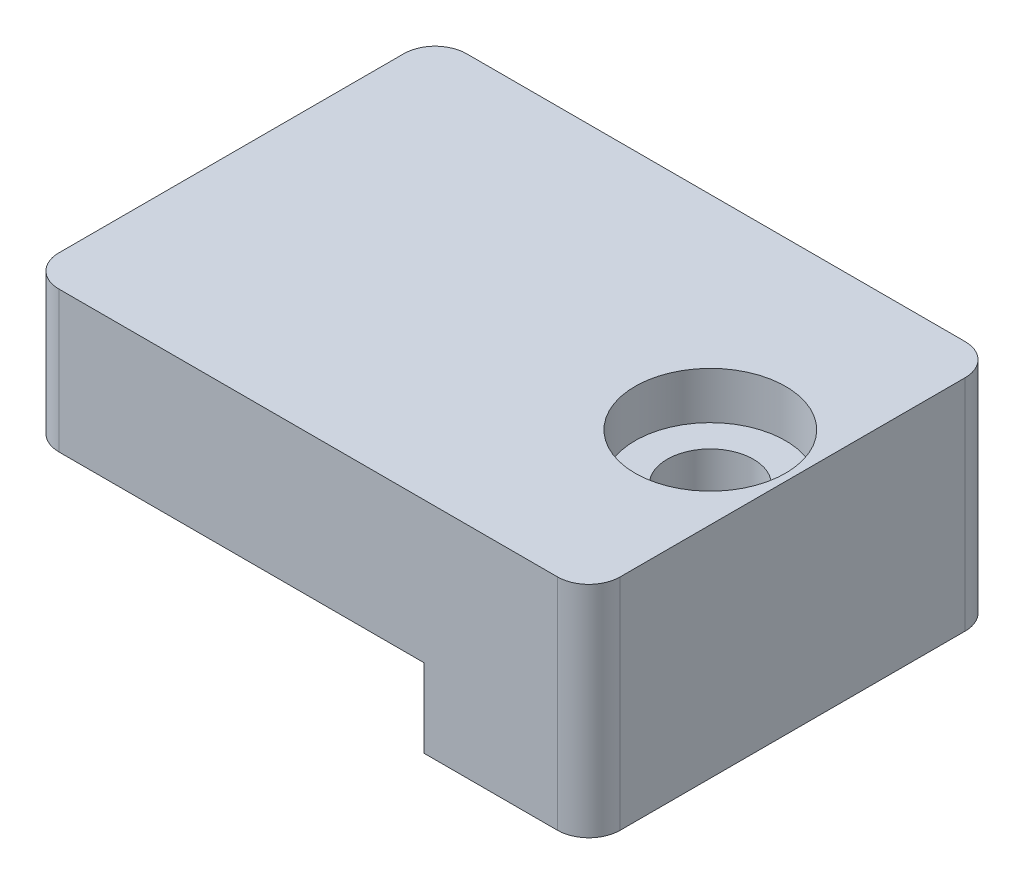
SolidWorks part; units mm, degrees
material "6061-T6 (SS)"
ref_plane "Front Plane" through (0, 0, 0) normal (0, 0, 1) x (1, 0, 0)
ref_plane "Top Plane" through (0, 0, 0) normal (0, 1, 0) x (1, 0, 0)
ref_plane "Right Plane" through (0, 0, 0) normal (1, 0, 0) x (0, 0, -1)
sketch "Sketch1" plane through (0, 0, 0) normal (0, 0, 1) x (1, 0, 0)
  line L0 (-25.3, 0) -> (-25.3, -9)
  line L1 (-25.3, -9) -> (0, -9)
  line L2 (0, -9) -> (0, -14)
  line L3 (0, -14) -> (10.5, -14)
  line L4 (10.5, -14) -> (10.5, 0)
  line L5 (10.5, 0) -> (0, 0)
  line L6 (0, 0) -> (-25.3, 0)
  dimension "D1" = 14
  dimension "D2" = 5
  dimension "D3" = 25.3
  dimension "D4" = 10.5
extrude "Boss-Extrude1" add sketch "Sketch1" along normal blind 26
sketch "Sketch2" plane through (0, 0, 0) normal (0, 1, 0) x (1, 0, 0)
  line L0 (-25.3, -13) -> (10.5, -13) construction
  line L1 (-25.3, -26) -> (-25.3, 0) construction
  line L2 (10.5, -26) -> (10.5, 0) construction
  line L3 (-21.3, -13) -> (-16.3, -13) construction
  line L4 (-21.3, -10.25) -> (-16.3, -10.25)
  line L5 (-21.3, -15.75) -> (-16.3, -15.75)
  arc A0 (-21.3, -10.25) -> (-21.3, -15.75) centre (-21.3, -13) ccw
  arc A1 (-16.3, -15.75) -> (-16.3, -10.25) centre (-16.3, -13) ccw
  point P8 (-18.8, -13)
  dimension "D1" = 2.75
  dimension "D2" = 4
  dimension "D3" = 5
extrude "Cut-Extrude1" [suppressed] cut sketch "Sketch2" against normal blind 19
fillet "Fillet1" [suppressed] radius 2
fillet "Fillet2" radius 2 4 edges at (10.5, -7, 26) (10.5, -7, 0) (-25.3, -4.5, 0) (-25.3, -4.5, 26)
sketch "Sketch4" [suppressed] plane through (-25.3, 0, 0) normal (-1, 0, 0) x (0, 0, 1)
  line L0 (8.625, -9) -> (8.625, -2.25)
  line L1 (24, -9) -> (2, -9) construction
  line L2 (8.625, -2.25) -> (17.375, -2.25)
  line L3 (17.375, -2.25) -> (17.375, -9)
  line L4 (0, -9) -> (26, -9) construction
  line L5 (17.375, -9) -> (8.625, -9)
  line L6 (8.625, -5.625) -> (2, -5.625) construction
  line L7 (2, 0) -> (2, -9) construction
  line L8 (17.375, -5.625) -> (24, -5.625) construction
  line L9 (24, -9) -> (24, 0) construction
  line L10 (5, -7.725) -> (2, -7.725) construction
  line L11 (5, -9) -> (21, -9)
  line L12 (5, -9) -> (5, -6.45)
  line L13 (5, -6.45) -> (21, -6.45)
  line L14 (21, -9) -> (21, -6.45)
  line L15 (5, -9) -> (21, -6.45) construction
  line L16 (5, -6.45) -> (21, -9) construction
  line L17 (21, -7.725) -> (24, -7.725) construction
  point P20 (13, -7.725)
  dimension "D1" = 8.75
  dimension "D2" = 4.2
  dimension "D3" = 16
  dimension "D4" = 6.75
extrude "Cut-Extrude2" [suppressed] cut sketch "Sketch4" against normal blind 23.3 contours L0 L13 L3 L2
sketch "Sketch6" plane through (0, -14, 0) normal (0, -1, 0) x (1, 0, 0)
  line L0 (0, 13) -> (10.5, 13) construction
  line L1 (0, 26) -> (0, 0) construction
  line L2 (10.5, 24) -> (10.5, 2) construction
  line L7 (8.5, 26) -> (-23.3, 26)
  line L8 (10.5, 2) -> (10.5, 24)
  line L9 (-23.3, 0) -> (8.5, 0)
  line L10 (-25.3, 24) -> (-25.3, 2)
  line L11 (8.5, 26) -> (-23.3, 26)
  line L12 (10.5, 2) -> (10.5, 24)
  line L13 (-23.3, 0) -> (8.5, 0)
  line L14 (-25.3, 24) -> (-25.3, 2)
  circle A0 centre (5.25, 13) radius 2.75
  arc A5 (10.5, 24) -> (8.5, 26) centre (8.5, 24) ccw
  arc A6 (8.5, 0) -> (10.5, 2) centre (8.5, 2) ccw
  arc A7 (-25.3, 2) -> (-23.3, 0) centre (-23.3, 2) ccw
  arc A8 (-23.3, 26) -> (-25.3, 24) centre (-23.3, 24) ccw
  arc A9 (10.5, 24) -> (8.5, 26) centre (8.5, 24) ccw
  arc A10 (8.5, 0) -> (10.5, 2) centre (8.5, 2) ccw
  arc A11 (-25.3, 2) -> (-23.3, 0) centre (-23.3, 2) ccw
  arc A12 (-23.3, 26) -> (-25.3, 24) centre (-23.3, 24) ccw
  dimension "D1" = 5.5
  dimension "D2" = 0
sketch "Sketch7" plane through (0, 0, 0) normal (0, 1, 0) x (1, 0, 0)
  circle A0 centre (5.25, -13) radius 2.75 construction
  circle A1 centre (5.25, -13) radius 2.75
hole_wizard "CBORE for M5 SBHCS1" positions "Sketch8" profile "Sketch9" counterbore size "M5" standard "ANSI Metric" end condition through all
sketch "Sketch8" plane through (0, 0, 0) normal (0, 1, 0) x (1, 0, 0)
  point P0 (5.25, -13)
sketch "Sketch9" plane through (5.25, 0, 13) normal (1, 0, 0) x (0, 0, 1)
  line L0 (0, 0) -> (0, 14)
  line L1 (0, 14) -> (2.75, 14)
  line L3 (2.75, 14) -> (2.75, 3)
  line L4 (2.75, 3) -> (4.8, 3)
  line L5 (4.8, 3) -> (4.8, 0)
  line L7 (4.8, 0) -> (0, 0)
  line L11 (0, -6.35) -> (0, 107.95) construction
  dimension "Thru Hole Dia." = 5.5
  dimension "Thru Hole Depth" = 14
  dimension "C'Bore Dia." = 9.6
  dimension "C'Bore Depth" = 3
fillet "Fillet5" [suppressed] radius 1
sketch "Sketch10" plane through (-25.3, 0, 0) normal (-1, 0, 0) x (0, 0, 1)
  line L0 (8.625, -6.45) -> (8.625, -2.25)
  line L1 (8.625, -2.25) -> (17.375, -2.25)
  line L2 (17.375, -2.25) -> (17.375, -6.45)
  line L3 (17.375, -6.45) -> (8.625, -6.45)
  line L4 (8.625, -4.35) -> (2, -4.35) construction
  line L5 (17.375, -4.35) -> (24, -4.35) construction
  line L6 (5, -7.725) -> (2, -7.725) construction
  line L7 (5, -9) -> (21, -9)
  line L8 (5, -9) -> (5, -6.45)
  line L9 (5, -6.45) -> (21, -6.45)
  line L10 (21, -9) -> (21, -6.45)
  line L11 (5, -9) -> (21, -6.45) construction
  line L12 (5, -6.45) -> (21, -9) construction
  line L13 (21, -7.725) -> (24, -7.725) construction
  line L14 (24, -9) -> (2, -9) construction
  line L15 (2, 0) -> (2, -9) construction
  line L16 (24, -9) -> (24, 0) construction
  point P12 (13, -7.725)
  point P17 (0, 0)
  point P22 (24, -4.5)
  point P25 (27.9256, -7.725)
  point P26 (24, -7.725)
  point P27 (8, -7.725)
  point P28 (8, -7.725)
  point P29 (8, -7.725)
  point P30 (2, -7.725)
  point P31 (3.5053, -4.5)
  point P32 (0, 0)
  point P33 (2, -4.35)
  point P34 (24, -4.35)
  line M15 (2, -9) -> (24, -9)
  dimension "D1" = 8.75
  dimension "D2" = 16
  dimension "D3" = 4.2
  dimension "D4" = 6.75
extrude "Cut-Extrude3" cut sketch "Sketch10" against normal blind 23.3 contours L10 L9 L3 L8 M15
fillet "Fillet6" radius 3.175 4 edges at (-2, -4.35, 17.375) (-2, -7.725, 21) (-2, -7.725, 5) (-2, -4.35, 8.625)
